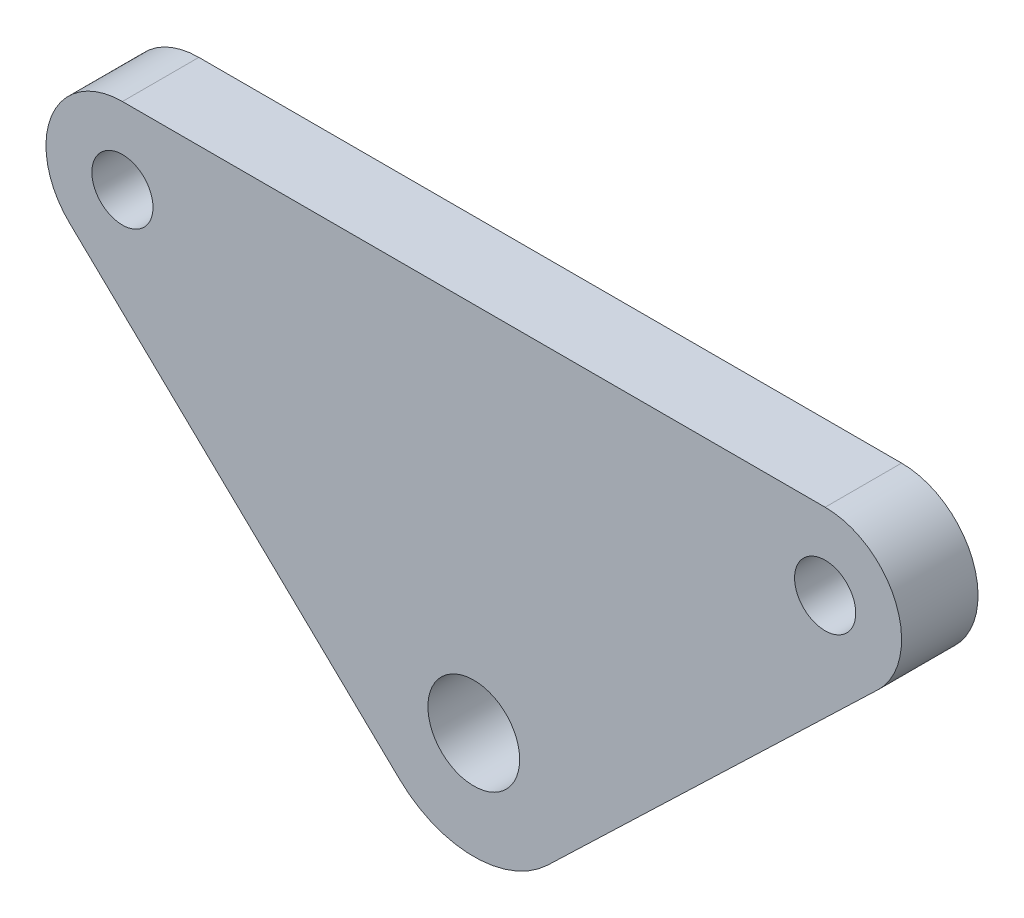
SolidWorks part; units mm, degrees
ref_plane "Front Plane" through (0, 0, 0) normal (0, 0, 1) x (1, 0, 0)
ref_plane "Top Plane" through (0, 0, 0) normal (0, 1, 0) x (1, 0, 0)
ref_plane "Right Plane" through (0, 0, 0) normal (1, 0, 0) x (0, 0, -1)
sketch "Sketch1" plane through (0, 0, 0) normal (0, 0, 1) x (1, 0, 0)
  line L3 (-125.3502, 161.2689) -> (-79.3875, 161.2689) construction
  line L4 (-75.9254, 152.6615) -> (-97.5219, 131.9349) construction
  line L5 (-128.8123, 152.6615) -> (-107.2159, 131.9349) construction
  line L6 (-125.3502, 161.2689) -> (-79.3875, 161.2689)
  line L7 (-75.9254, 152.6615) -> (-97.5219, 131.9349)
  line L8 (-128.8123, 152.6615) -> (-107.2159, 131.9349)
  circle A9 centre (-102.3689, 136.9853) radius 3 construction
  circle A10 centre (-79.3875, 156.2689) radius 2 construction
  circle A11 centre (-125.3502, 156.2689) radius 2 construction
  arc A12 (-75.9254, 152.6615) -> (-79.3875, 161.2689) centre (-79.3875, 156.2689) ccw construction
  arc A13 (-107.2159, 131.9349) -> (-97.5219, 131.9349) centre (-102.3689, 136.9853) ccw construction
  arc A14 (-125.3502, 161.2689) -> (-128.8123, 152.6615) centre (-125.3502, 156.2689) ccw construction
  circle A15 centre (-102.3689, 136.9853) radius 3
  circle A16 centre (-79.3875, 156.2689) radius 2
  circle A17 centre (-125.3502, 156.2689) radius 2
  arc A18 (-75.9254, 152.6615) -> (-79.3875, 161.2689) centre (-79.3875, 156.2689) ccw
  arc A19 (-107.2159, 131.9349) -> (-97.5219, 131.9349) centre (-102.3689, 136.9853) ccw
  arc A20 (-125.3502, 161.2689) -> (-128.8123, 152.6615) centre (-125.3502, 156.2689) ccw
extrude "Boss-Extrude1" add sketch "Sketch1" against normal blind 5 from offset 10
